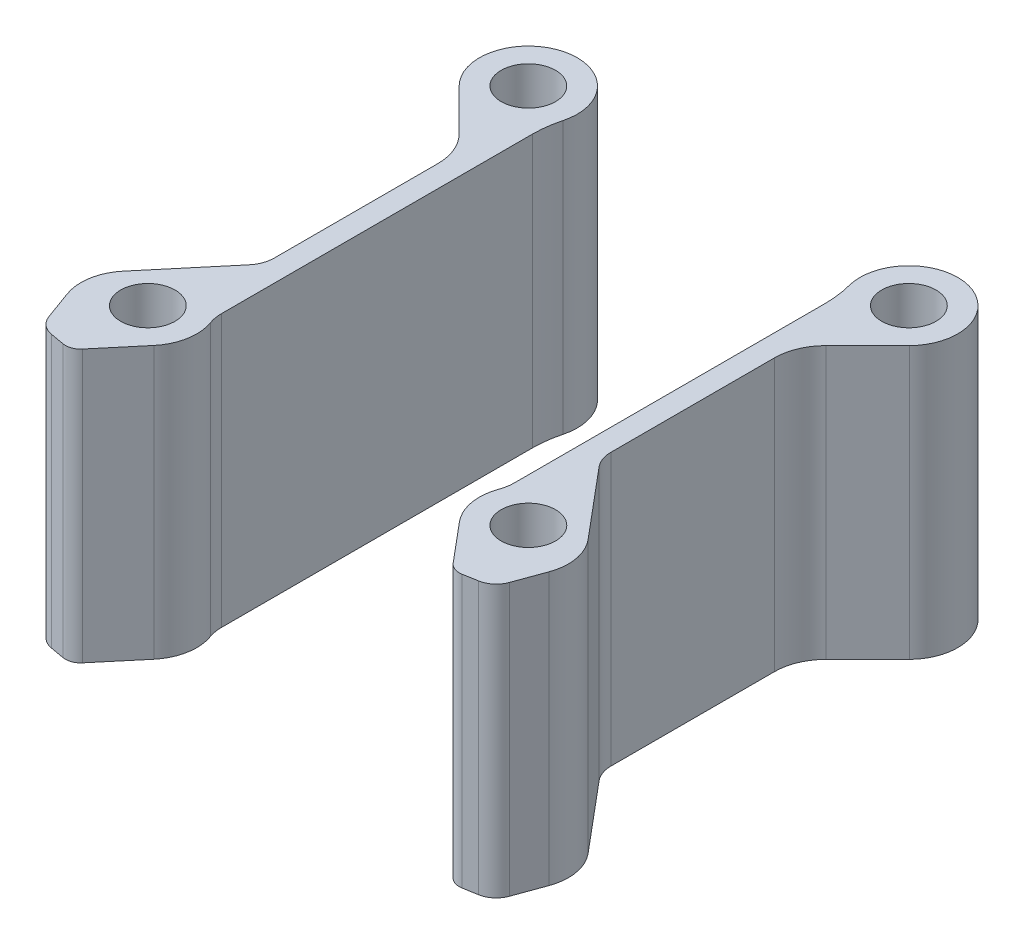
SolidWorks part; units mm, degrees
ref_plane "Front Plane" through (0, 0, 0) normal (0, 0, 1) x (1, 0, 0)
ref_plane "Top Plane" through (0, 0, 0) normal (0, 1, 0) x (1, 0, 0)
ref_plane "Right Plane" through (0, 0, 0) normal (1, 0, 0) x (0, 0, -1)
sketch "Sketch1" plane through (0, 0, 0) normal (0, 1, 0) x (1, 0, 0)
  line L0 (0.1059, 21.2801) -> (0.1059, 16.2801) construction
  line L1 (0.1059, -13.7199) -> (0.1059, -18.7199) construction
  line L8 (-3.3413, -19.1124) -> (-0.3389, -22.6905)
  line L16 (0.9581, -23.1626) -> (2.2498, -22.9348)
  line L24 (3.7819, -21.6492) -> (4.7588, -18.9652)
  line L32 (3.9906, -14.6105) -> (-1.2964, -8.3116)
  line L38 (-1.9161, -6.6092) -> (-1.9161, 8.4321)
  line L44 (-0.5286, 11.7818) -> (3.3082, 15.6186)
  line L74 (-3.9161, 15.1228) -> (-3.9161, -13.4772)
  line L79 (-17.3941, 28.7072) -> (-17.3941, -28.1732) construction
  line L80 (-34.8941, -13.7199) -> (-34.8941, -18.7199) construction
  line L81 (-34.8941, 21.2801) -> (-34.8941, 16.2801) construction
  line L82 (-30.8721, 15.1228) -> (-30.8721, -13.4772)
  line L83 (-34.2595, 11.7818) -> (-38.0964, 15.6186)
  line L84 (-32.8721, -6.6092) -> (-32.8721, 8.4321)
  line L85 (-38.7788, -14.6105) -> (-33.4918, -8.3116)
  line L86 (-38.5701, -21.6492) -> (-39.547, -18.9652)
  line L87 (-35.7463, -23.1626) -> (-37.038, -22.9348)
  line L88 (-31.4469, -19.1124) -> (-34.4493, -22.6905)
  circle A0 centre (0.1059, 18.7801) radius 2.5
  circle A1 centre (0.1059, -16.2199) radius 2.5
  arc A3 (-3.9161, -13.4772) -> (-4.1288, -14.6977) centre (-7.5245, -13.4772) cw
  arc A4 (-4.1288, -14.6977) -> (-3.3413, -19.1124) centre (0.1059, -16.2199) ccw
  arc A5 (-0.3389, -22.6905) -> (0.9581, -23.1626) centre (0.7184, -21.8033) ccw
  arc A6 (2.2498, -22.9348) -> (3.7819, -21.6492) centre (1.9025, -20.9652) ccw
  arc A7 (3.9906, -14.6105) -> (4.7588, -18.9652) centre (0.604, -17.453) cw
  arc A8 (-1.9161, -6.6092) -> (-1.2964, -8.3116) centre (0.7318, -6.6092) ccw
  arc A9 (-0.5286, 11.7818) -> (-1.9161, 8.4321) centre (2.821, 8.4321) ccw
  arc A12 (-4.243, 17.6237) -> (-3.9161, 15.1228) centre (-13.6477, 15.1228) cw
  arc A13 (3.3082, 15.6186) -> (-4.243, 17.6237) centre (0.1059, 18.7801) ccw
  arc A14 (-38.0964, 15.6186) -> (-30.5452, 17.6237) centre (-34.8941, 18.7801) cw
  arc A15 (-30.5452, 17.6237) -> (-30.8721, 15.1228) centre (-21.1405, 15.1228) ccw
  arc A16 (-34.2595, 11.7818) -> (-32.8721, 8.4321) centre (-37.6092, 8.4321) cw
  arc A17 (-32.8721, -6.6092) -> (-33.4918, -8.3116) centre (-35.52, -6.6092) cw
  arc A18 (-38.7788, -14.6105) -> (-39.547, -18.9652) centre (-35.3922, -17.453) ccw
  arc A19 (-37.038, -22.9348) -> (-38.5701, -21.6492) centre (-36.6907, -20.9652) cw
  arc A20 (-34.4493, -22.6905) -> (-35.7463, -23.1626) centre (-35.5066, -21.8033) cw
  arc A21 (-30.6594, -14.6977) -> (-31.4469, -19.1124) centre (-34.8941, -16.2199) cw
  arc A22 (-30.8721, -13.4772) -> (-30.6594, -14.6977) centre (-27.2637, -13.4772) ccw
  circle A23 centre (-34.8941, -16.2199) radius 2.5
  circle A24 centre (-34.8941, 18.7801) radius 2.5
  dimension "D1" = 5
  dimension "D2" = 5
  dimension "D3" = 2
  dimension "D7" = 4.5
  dimension "D8" = 4.5
  dimension "D4" = 28.6
  dimension "D5" = 17.5
  dimension "D6" = 35
extrude "Boss-Extrude1" add sketch "Sketch1" along normal blind 25
